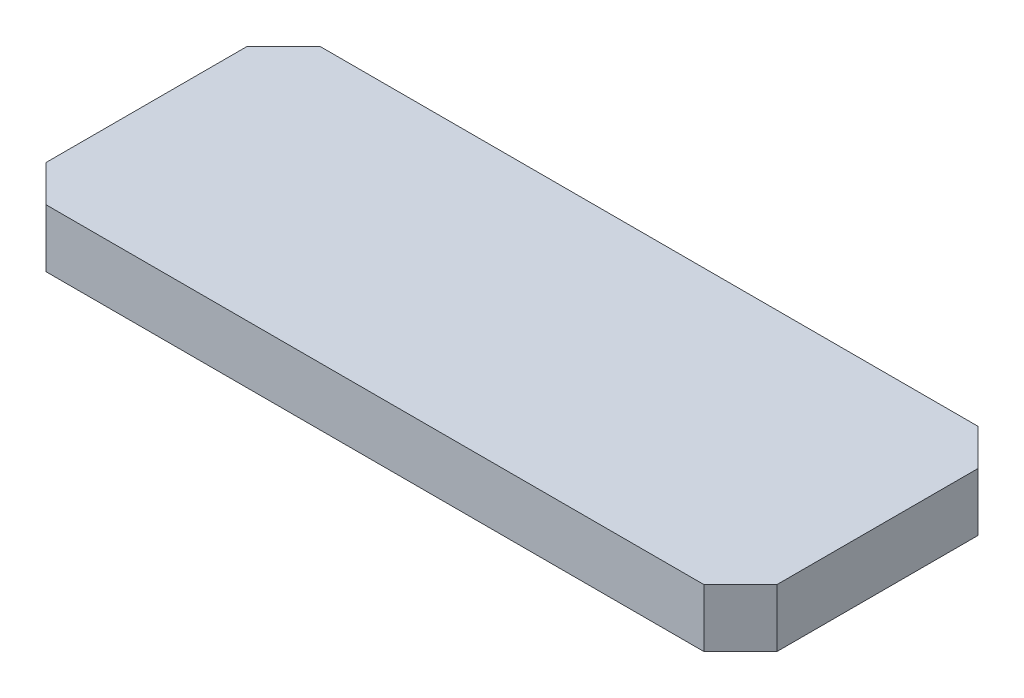
SolidWorks part; units mm, degrees
material "Silicon Rubber"
ref_plane "Front" through (0, 0, 0) normal (0, 0, 1) x (1, 0, 0)
ref_plane "Top" through (0, 0, 0) normal (0, 1, 0) x (1, 0, 0)
ref_plane "Right" through (0, 0, 0) normal (1, 0, 0) x (0, 0, -1)
sketch "Sketch1" plane through (0, 0, 0) normal (0, 1, 0) x (1, 0, 0)
  line L1 (0, 0) -> (40, 0)
  line L2 (0, 0) -> (0, 15)
  line L3 (0, 15) -> (40, 15)
  line L4 (40, 0) -> (40, 15)
  dimension "D1" = 40
  dimension "D2" = 15
extrude "Boss-Extrude1" add sketch "Sketch1" along normal blind 3.175
chamfer "Chamfer1" distance 2 angle 45 4 edges at (0, 1.5875, -15) (40, 1.5875, -15) (40, 1.5875, 0) (0, 1.5875, 0)
